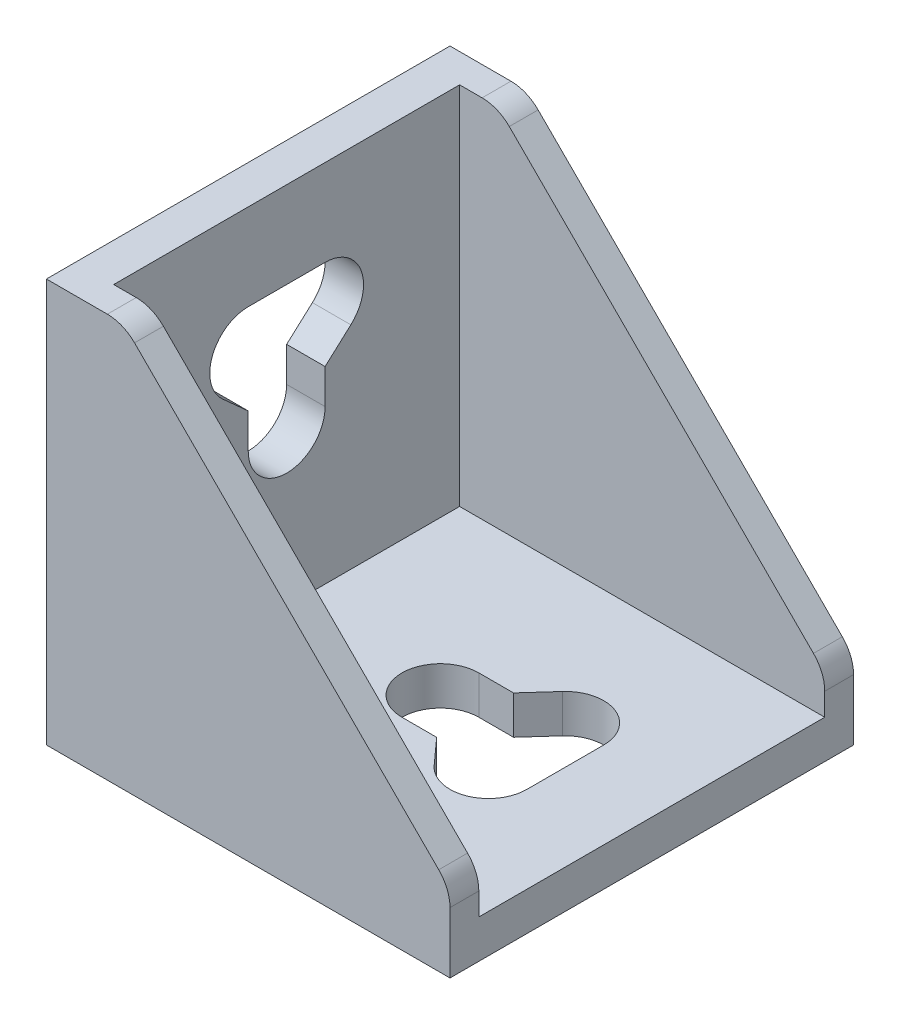
SolidWorks part; units mm, degrees
material "Алюминиевый сплав"
ref_plane "Спереди" through (0, 0, 0) normal (0, 0, 1) x (1, 0, 0)
ref_plane "Сверху" through (0, 0, 0) normal (0, 1, 0) x (1, 0, 0)
ref_plane "Справа" through (0, 0, 0) normal (1, 0, 0) x (0, 0, -1)
sketch "Эскиз1" plane through (0, 0, 0) normal (0, 0, 1) x (1, 0, 0)
  line L0 (0, 42) -> (0, 0)
  line L1 (0, 0) -> (42, 0)
  line L2 (42, 0) -> (42, 4)
  line L4 (4, 42) -> (0, 42)
  line L5 (4, 42) -> (4, 4)
  line L6 (4, 4) -> (42, 4)
  dimension "D1" = 42
  dimension "D2" = 4
extrude "Бобышка-Вытянуть1" add sketch "Эскиз1" along normal mid plane 42
sketch "Эскиз2" plane through (0, 0, 21) normal (0, 0, 1) x (1, 0, 0)
  line L1 (42, 4) -> (4, 4)
  line L2 (4, 4) -> (4, 42)
  line L3 (4, 42) -> (8, 42)
  line L4 (8, 42) -> (42, 8)
  line L5 (42, 8) -> (42, 4)
  line L6 (42, 0) -> (42, 4) construction
extrude "Бобышка-Вытянуть2" add sketch "Эскиз2" against normal blind 3
fillet "Скругление1" radius 4 2 edges at (42, 8, 19.5) (8, 42, 19.5)
mirror "Зеркальное отражение2" about plane through (0, 0, 0) normal (0, 0, 1) of "Бобышка-Вытянуть2", "Скругление1"
sketch "Эскиз3" plane through (0, 4, 0) normal (0, 1, 0) x (1, 0, 0)
  line L0 (20, 4) -> (23.6111, 4)
  line L4 (23.6111, 4) -> (26.0309, 6.6804)
  line L5 (33, 4) -> (33, -4)
  line L6 (26.0309, -6.6804) -> (23.6111, -4)
  line L7 (23.6111, -4) -> (20, -4)
  line L8 (42, -18) -> (42, 18) construction
  arc A2 (20, 4) -> (20, -4) centre (20, 0) ccw
  arc A3 (26.0309, 6.6804) -> (33, 4) centre (29, 4) cw
  arc A4 (33, -4) -> (26.0309, -6.6804) centre (29, -4) cw
  point P15 (33, 0)
  dimension "D2" = 8
  dimension "D3" = 4
  dimension "D4" = 9
  dimension "D1" = 13
extrude "Вырез-Вытянуть1" cut sketch "Эскиз3" against normal through all
sketch "Эскиз4" plane through (0, 0, 0) normal (0, 0, 1) x (1, 0, 0)
  line L0 (1.2322, 0) -> (0, -1.2322)
  line L1 (0, 0) -> (42, 0) construction
  line L2 (0, -1.2322) -> (1.7678, -3)
  line L3 (1.7678, -3) -> (4.7678, 0)
  line L4 (4.7678, 0) -> (1.2322, 0)
  line L5 (42, 0) -> (39, -3)
  line L6 (39, -3) -> (37.2322, -1.2322)
  line L7 (37.2322, -1.2322) -> (38.4645, 0)
  line L8 (38.4645, 0) -> (42, 0)
  line L9 (0, 42) -> (0, 0) construction
  dimension "D1" = 3
  dimension "D2" = 45
  dimension "D3" = 2.5
extrude "Бобышка-Вытянуть3" add sketch "Эскиз4" along normal mid plane 9.5
ref_plane "Плоскость1" through (0, 0, 0) normal (-0.7071, 0.7071, 0) x (0.7071, 0.7071, 0)
mirror "Зеркальное отражение3" about plane through (0, 0, 0) normal (-0.7071, 0.7071, 0) of "Бобышка-Вытянуть3", "Вырез-Вытянуть1"
